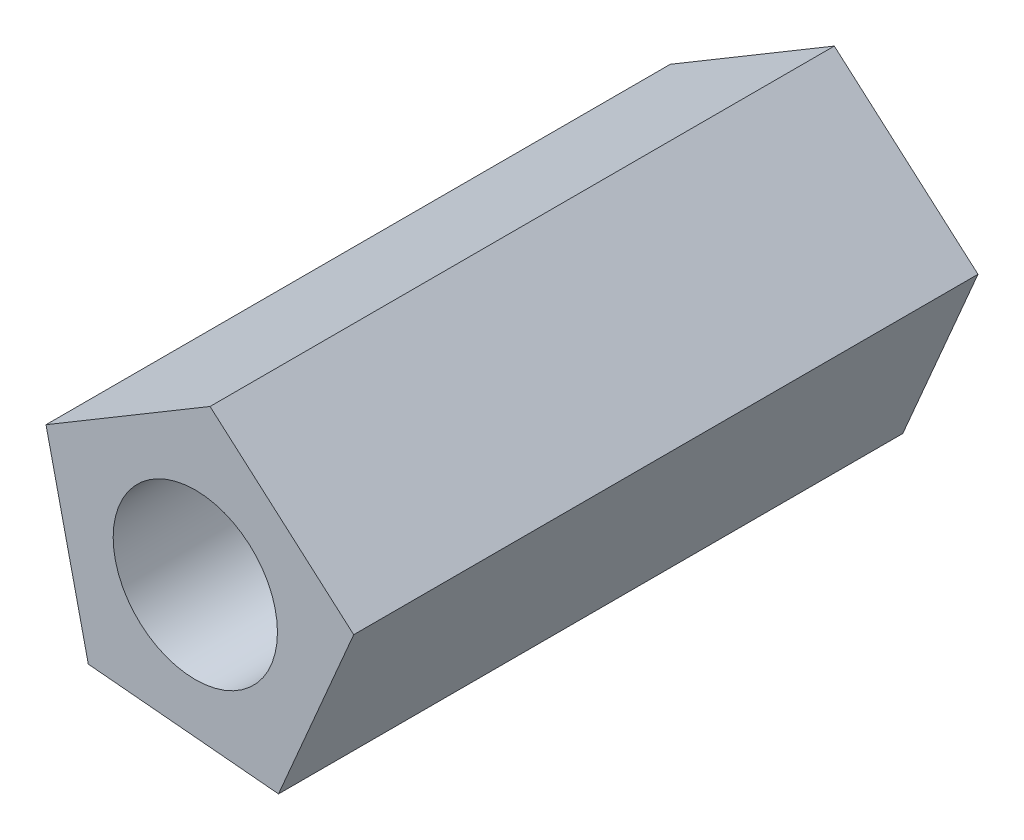
SolidWorks part; units mm, degrees
material "Alüminyum Bronz"
ref_plane "Ön Düzlem" through (0, 0, 0) normal (0, 0, 1) x (1, 0, 0)
ref_plane "Üst Düzlem" through (0, 0, 0) normal (0, 1, 0) x (1, 0, 0)
ref_plane "Sağ Düzlem" through (0, 0, 0) normal (1, 0, 0) x (0, 0, -1)
sketch "Çizim1" plane through (0, 0, 0) normal (0, 0, 1) x (1, 0, 0)
  line L1 (0.448, 4.9239) -> (-4.5445, 1.9476)
  line L2 (-4.5445, 1.9476) -> (-3.2566, -3.7202)
  line L3 (-3.2566, -3.7202) -> (2.5318, -4.2469)
  line L4 (2.5318, -4.2469) -> (4.8214, 1.0955)
  line L5 (4.8214, 1.0955) -> (0.448, 4.9239)
  circle A0 centre (0, 0) radius 2.5
  circle A1 centre (0, 0) radius 4 construction
extrude "Yükseklik-Ekstrüzyon1" add sketch "Çizim1" along normal blind 19
